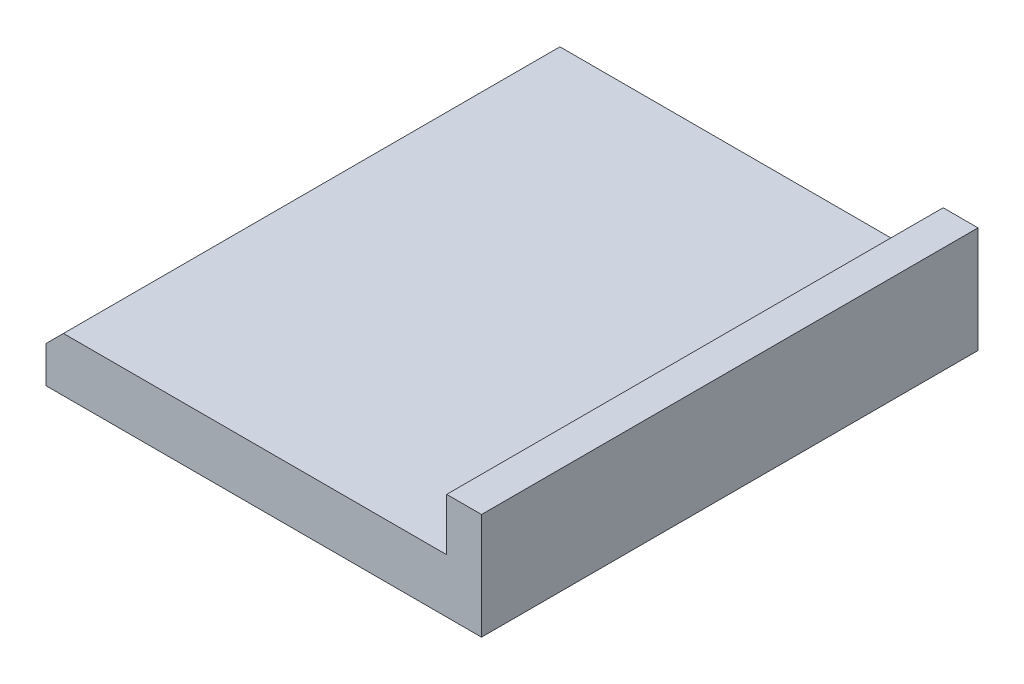
SolidWorks part; units mm, degrees
ref_plane "Front Plane" through (0, 0, 0) normal (0, 0, 1) x (1, 0, 0)
ref_plane "Top Plane" through (0, 0, 0) normal (0, 1, 0) x (1, 0, 0)
ref_plane "Right Plane" through (0, 0, 0) normal (1, 0, 0) x (0, 0, -1)
sketch "Sketch1" plane through (0, 0, 0) normal (0, 1, 0) x (1, 0, 0)
  line L1 (-15.8056, 12.6783) -> (9.1944, 12.6783)
  line L2 (-15.8056, 12.6783) -> (-15.8056, -15.8217)
  line L3 (-15.8056, -15.8217) -> (9.1944, -15.8217)
  line L4 (9.1944, 12.6783) -> (9.1944, -15.8217)
  dimension "D1" = 28.5
  dimension "D2" = 25
extrude "Boss-Extrude1" add sketch "Sketch1" along normal blind 3.3
sketch "Sketch2" plane through (0, 3.3, 0) normal (0, 1, 0) x (1, 0, 0)
  line L0 (-15.8056, -15.8217) -> (9.1944, -15.8217) construction
  line L1 (9.1944, 12.6783) -> (7.1944, 12.6783)
  line L2 (9.1944, 12.6783) -> (9.1944, -15.8217)
  line L3 (9.1944, -15.8217) -> (7.1944, -15.8217)
  line L4 (7.1944, 12.6783) -> (7.1944, -15.8217)
  dimension "D1" = 2
extrude "Boss-Extrude2" add sketch "Sketch2" along normal blind 3
chamfer "Chamfer1" distance 1 angle 45 1 edges at (-15.8056, 3.3, 1.5717)
sketch "Sketch3" plane through (0, 0, 0) normal (0, -1, 0) x (1, 0, 0)
  circle A0 centre (-2.8478, 0) radius 21.8916
extrude "Cut-Extrude1" cut sketch "Sketch3" against normal blind 0.2
